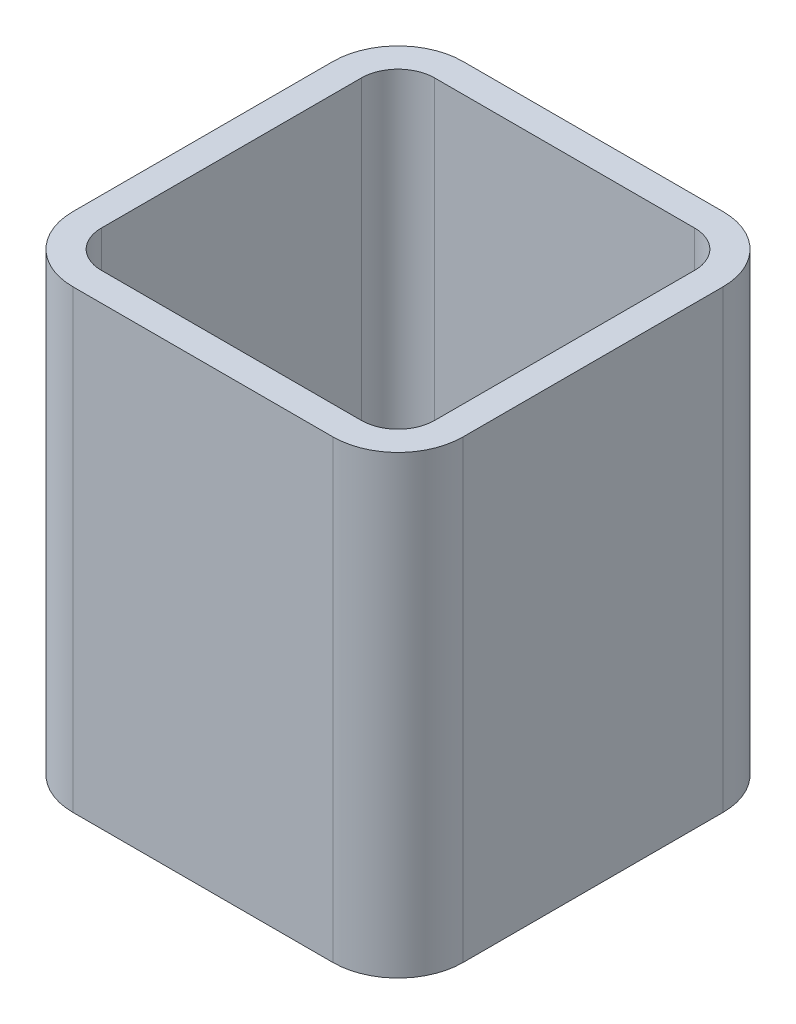
SolidWorks part; units mm, degrees
ref_plane "Front Plane" through (0, 0, 0) normal (0, 0, 1) x (1, 0, 0)
ref_plane "Top Plane" through (0, 0, 0) normal (0, 1, 0) x (1, 0, 0)
ref_plane "Right Plane" through (0, 0, 0) normal (1, 0, 0) x (0, 0, -1)
sketch "Sketch2" plane through (0, 0, 0) normal (0, 1, 0) x (1, 0, 0)
  line L1 (-101.6, 152.4) -> (101.6, 152.4)
  line L2 (-152.4, 101.6) -> (-152.4, -101.6)
  line L3 (-101.6, -152.4) -> (101.6, -152.4)
  line L4 (152.4, 101.6) -> (152.4, -101.6)
  line L5 (-152.4, 152.4) -> (152.4, -152.4) construction
  line L6 (-152.4, -152.4) -> (152.4, 152.4) construction
  arc A0 (101.6, 152.4) -> (152.4, 101.6) centre (101.6, 101.6) cw
  arc A1 (101.6, -152.4) -> (152.4, -101.6) centre (101.6, -101.6) ccw
  arc A2 (-152.4, -101.6) -> (-101.6, -152.4) centre (-101.6, -101.6) ccw
  arc A3 (-101.6, 152.4) -> (-152.4, 101.6) centre (-101.6, 101.6) ccw
  point P0 (0, 0)
  dimension "D3" = 50.8
  dimension "D1" = 304.8
  dimension "D2" = 304.8
extrude "Extrude-Thin1" add sketch "Sketch2" along normal blind 355.6 thin
